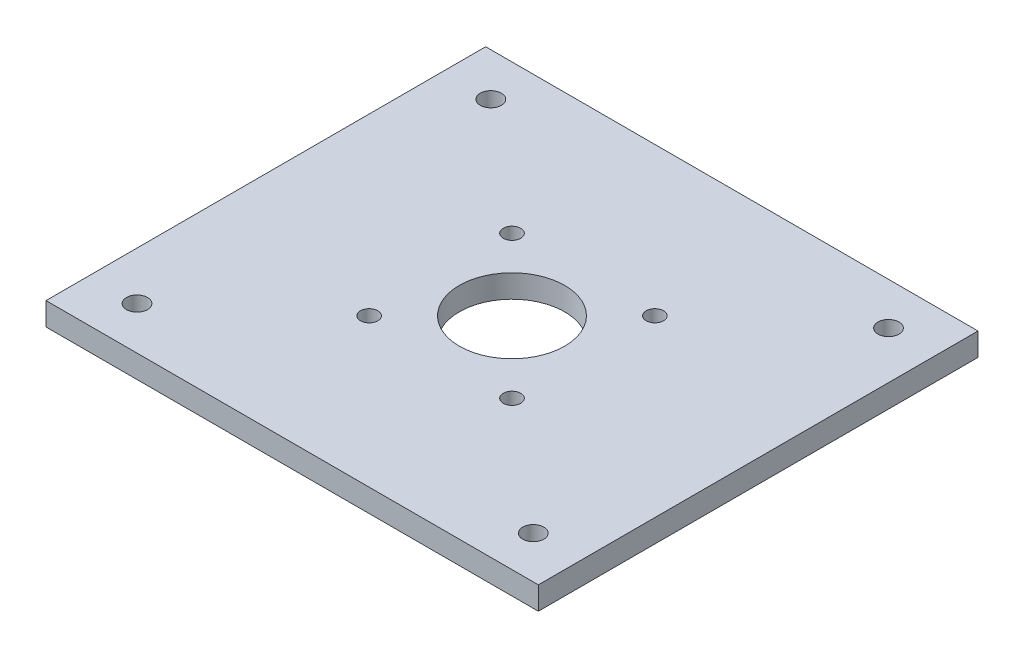
SolidWorks part; units mm, degrees
ref_plane "Front Plane" through (0, 0, 0) normal (0, 0, 1) x (1, 0, 0)
ref_plane "Top Plane" through (0, 0, 0) normal (0, 1, 0) x (1, 0, 0)
ref_plane "Right Plane" through (0, 0, 0) normal (1, 0, 0) x (0, 0, -1)
sketch "Sketch1" plane through (0, 0, 0) normal (0, 1, 0) x (1, 0, 0)
  line L1 (-53.75, -48) -> (53.75, -48)
  line L2 (-53.75, -48) -> (-53.75, 48)
  line L3 (-53.75, 48) -> (53.75, 48)
  line L4 (53.75, -48) -> (53.75, 48)
  line L5 (-53.75, -48) -> (53.75, 48) construction
  line L6 (-53.75, 48) -> (53.75, -48) construction
  point P0 (0, 0)
sketch "Sketch2" plane through (0, 0, 0) normal (0, 1, 0) x (1, 0, 0)
  line L1 (-53.75, -48) -> (53.75, 48) construction
  line L4 (-53.75, 48) -> (53.75, -48) construction
  circle A4 centre (-15.6, 15.6) radius 1.9
  circle A5 centre (15.6, 15.6) radius 1.9
  circle A6 centre (15.6, -15.6) radius 1.9
  circle A7 centre (-15.6, -15.6) radius 1.9
  circle A8 centre (0, 0) radius 11.5
  circle A9 centre (-43.2555, -38.6282) radius 2.3
  circle A10 centre (43.4257, 38.7802) radius 2.3
  circle A11 centre (-43.2555, 38.6282) radius 2.3
  circle A12 centre (43.4257, -38.7802) radius 2.3
  point P0 (0, 0)
  point P9 (0, 0)
extrude "Boss-Extrude1" add sketch "Sketch1" along normal blind 5 contours L2 L3 L4 L1
extrude "Cut-Extrude3" cut sketch "Sketch2" along normal blind 5
